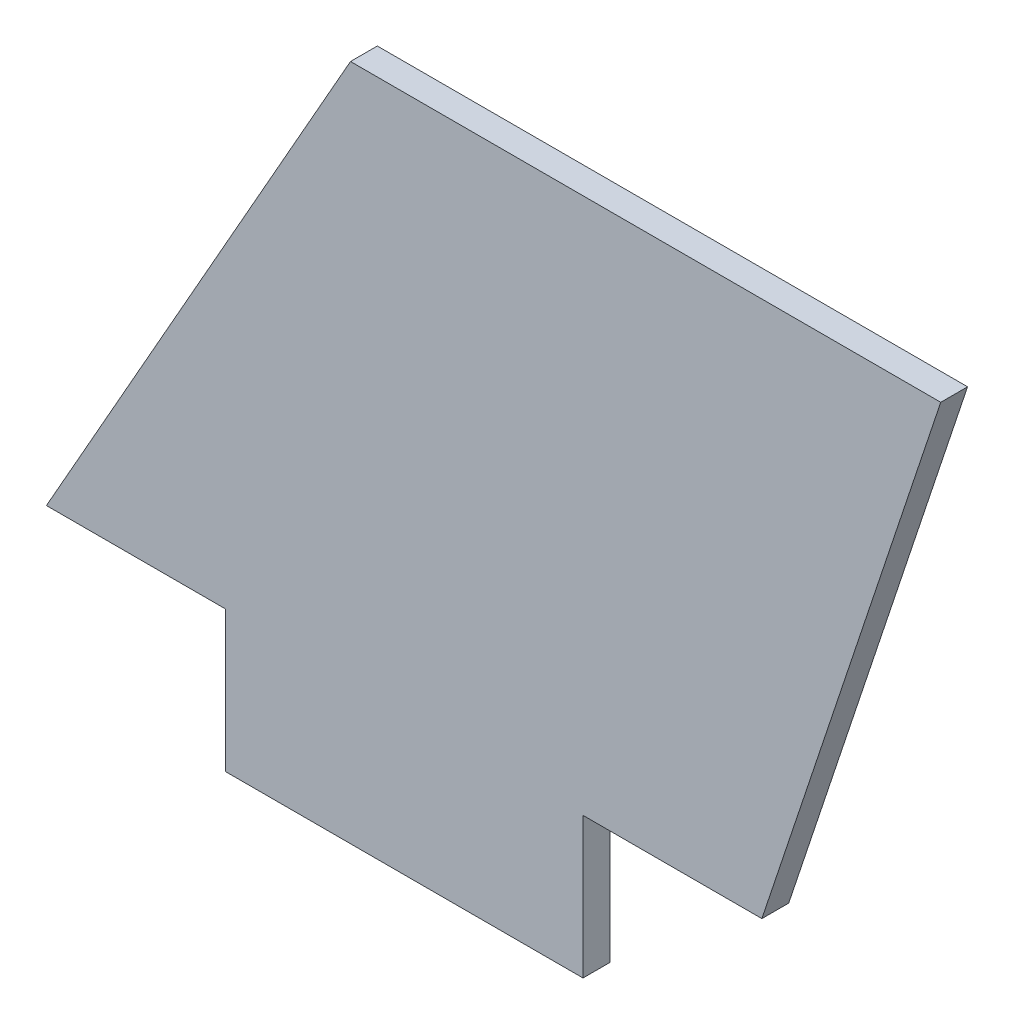
SolidWorks part; units mm, degrees
ref_plane "Front Plane" through (0, 0, 0) normal (0, 0, 1) x (1, 0, 0)
ref_plane "Top Plane" through (0, 0, 0) normal (0, 1, 0) x (1, 0, 0)
ref_plane "Right Plane" through (0, 0, 0) normal (1, 0, 0) x (0, 0, -1)
sketch "Sketch1" plane through (0, 0, 0) normal (0, 0, 1) x (1, 0, 0)
  line L0 (0, 0) -> (10, 0)
  line L1 (10, 0) -> (10, -7.875)
  line L2 (10, -7.875) -> (30, -7.875)
  line L3 (30, -7.875) -> (30, 0)
  line L4 (30, 0) -> (40, 0)
  line L5 (40, 0) -> (50, 30)
  line L6 (50, 30) -> (17, 30)
  line L7 (17, 30) -> (0, 0)
  dimension "D1" = 40
  dimension "D2" = 7.875
  dimension "D3" = 20
  dimension "D4" = 17
  dimension "D5" = 33
  dimension "D6" = 10
  dimension "D7" = 30
extrude "Boss-Extrude1" add sketch "Sketch1" along normal blind 1.5
